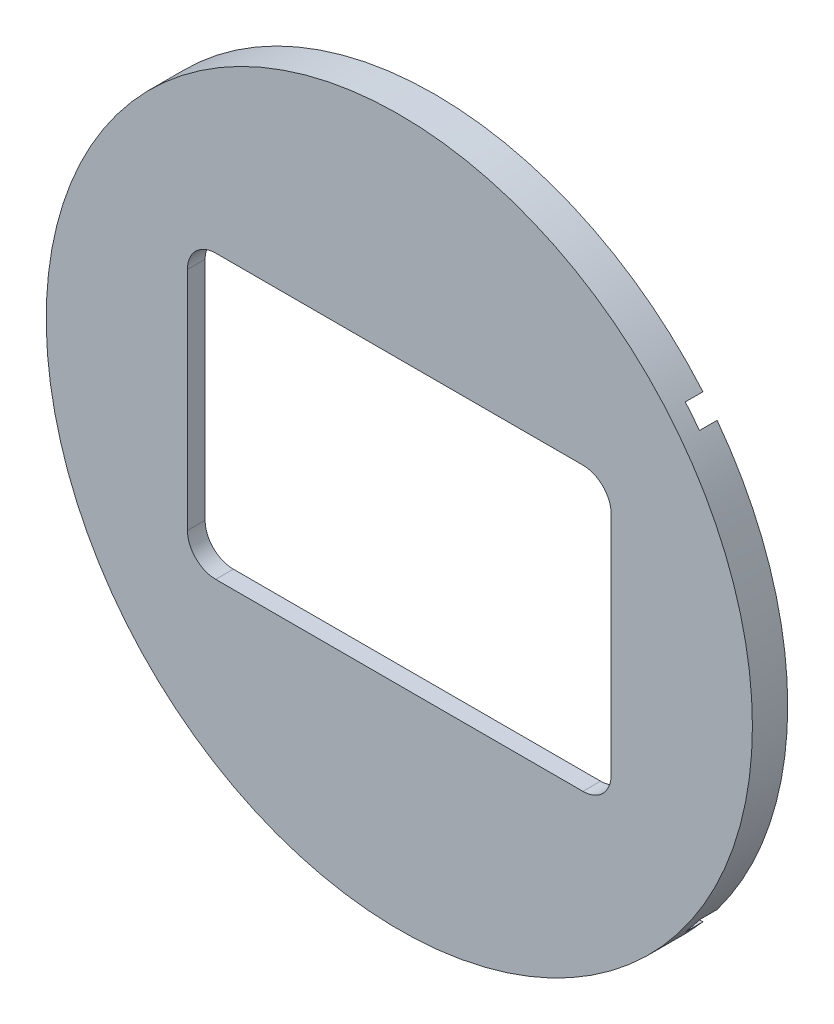
SolidWorks part; units mm, degrees
material "ABS PC"
ref_plane "Front Plane" through (0, 0, 0) normal (0, 0, 1) x (1, 0, 0)
ref_plane "Top Plane" through (0, 0, 0) normal (0, 1, 0) x (1, 0, 0)
ref_plane "Right Plane" through (0, 0, 0) normal (1, 0, 0) x (0, 0, -1)
sketch "Sketch1" plane through (0, 0, 0) normal (0, 0, 1) x (1, 0, 0)
  circle A0 centre (0, 0) radius 31.75
extrude "Boss-Extrude1" add sketch "Sketch1" along normal mid plane 3.175
sketch "Sketch3" plane through (0, 0, -1.5875) normal (0, 0, -1) x (-1, 0, 0)
  line L1 (-25.4, -20.6375) -> (25.4, -20.6375)
  line L2 (-25.4, -20.6375) -> (-25.4, 20.6375)
  line L3 (-25.4, 20.6375) -> (25.4, 20.6375)
  line L4 (25.4, -20.6375) -> (25.4, 20.6375)
  line L5 (-25.4, -20.6375) -> (25.4, 20.6375) construction
  line L6 (-25.4, 20.6375) -> (25.4, -20.6375) construction
  point P0 (0, 0)
  dimension "D1" = 41.275
  dimension "D2" = 50.8
extrude "Cut-Extrude1" cut sketch "Sketch3" against normal blind 1.5875
sketch "Sketch4" plane through (0, 0, 0) normal (0, 0, -1) x (-1, 0, 0)
  line L1 (-19.05, -12.7) -> (19.05, -12.7)
  line L2 (-19.05, -12.7) -> (-19.05, 12.7)
  line L3 (-19.05, 12.7) -> (19.05, 12.7)
  line L4 (19.05, -12.7) -> (19.05, 12.7)
  line L5 (-19.05, -12.7) -> (19.05, 12.7) construction
  line L6 (-19.05, 12.7) -> (19.05, -12.7) construction
  point P0 (0, 0)
  dimension "D1" = 38.1
  dimension "D2" = 25.4
extrude "Cut-Extrude2" cut sketch "Sketch4" against normal up to next
fillet "Fillet3" radius 2.54 4 edges at (-19.05, -12.7, 0.7937) (-19.05, 12.7, 0.7937) (19.05, -12.7, 0.7937) (19.05, 12.7, 0.7937)
